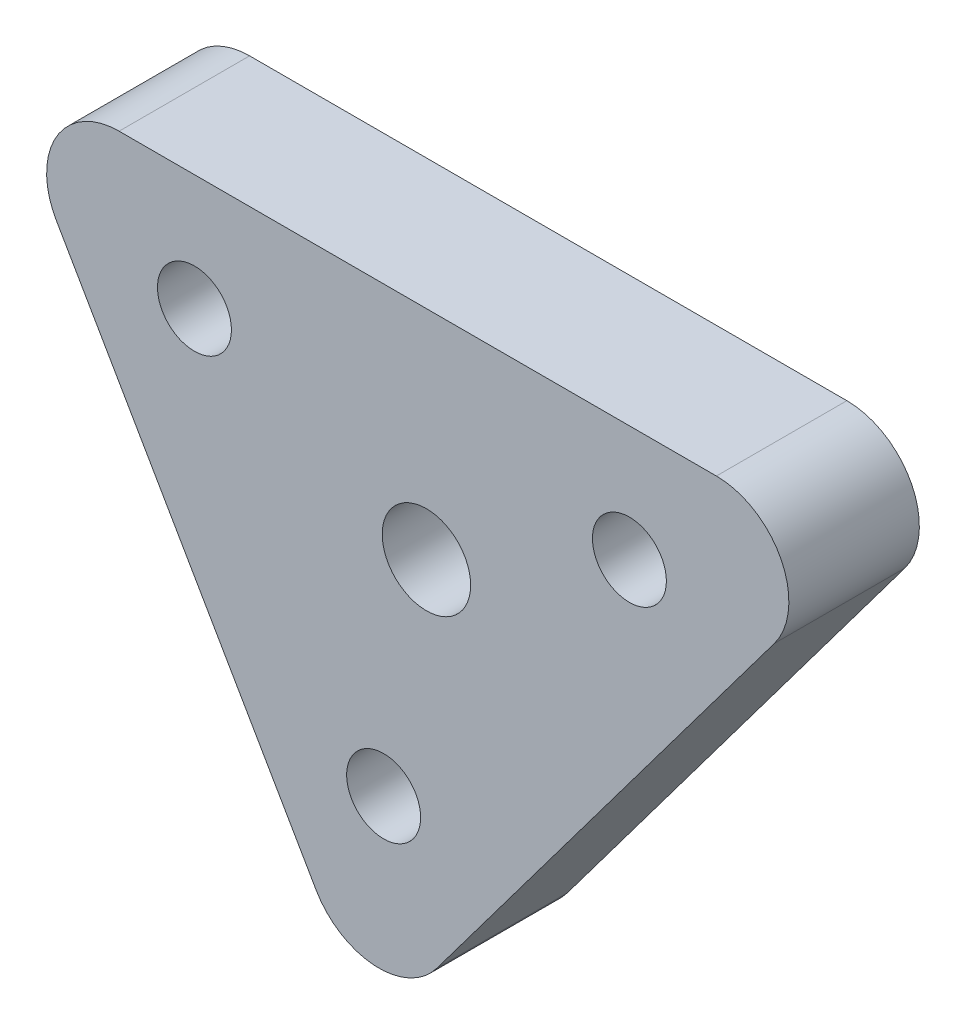
SolidWorks part; units mm, degrees
ref_plane "前视基准面" through (0, 0, 0) normal (0, 0, 1) x (1, 0, 0)
ref_plane "上视基准面" through (0, 0, 0) normal (0, 1, 0) x (1, 0, 0)
ref_plane "右视基准面" through (0, 0, 0) normal (1, 0, 0) x (0, 0, -1)
sketch "草图1" plane through (0, 0, 0) normal (0, 0, 1) x (1, 0, 0)
  line L0 (-40.197, 19.3205) -> (-10.197, 19.3205) construction
  line L1 (-54.0535, 27.3205) -> (5.803, 27.3205)
  line L2 (-27.1481, -3.2809) -> (-40.197, 19.3205) construction
  line L3 (-40.197, 19.3205) -> (-40.197, -20.6795) construction
  line L4 (-40.197, -20.6795) -> (-10.197, 19.3205) construction
  line L5 (5.803, 27.3205) -> (-28.018, -17.7741)
  line L6 (-28.018, -17.7741) -> (-54.0535, 27.3205)
  circle A0 centre (-40.197, 19.3205) radius 2.55
  circle A1 centre (-27.1481, -3.2809) radius 2.55
  circle A2 centre (-10.197, 19.3205) radius 2.55
  circle A3 centre (-24.197, 12.3205) radius 3.05
  dimension "D4" = 5.1
  dimension "D9" = 15
  dimension "D10" = 6.1
  dimension "D1" = 60
  dimension "D2" = 30
  dimension "D3" = 40
  dimension "D5" = 8
  dimension "D6" = 8
  dimension "D7" = 8
  dimension "D8" = 15
extrude "凸台-拉伸1" add sketch "草图1" along normal blind 9
fillet "圆角1" radius 5 3 edges at (-28.018, -17.7741, 4.5) (5.803, 27.3205, 4.5) (-54.0535, 27.3205, 4.5)
